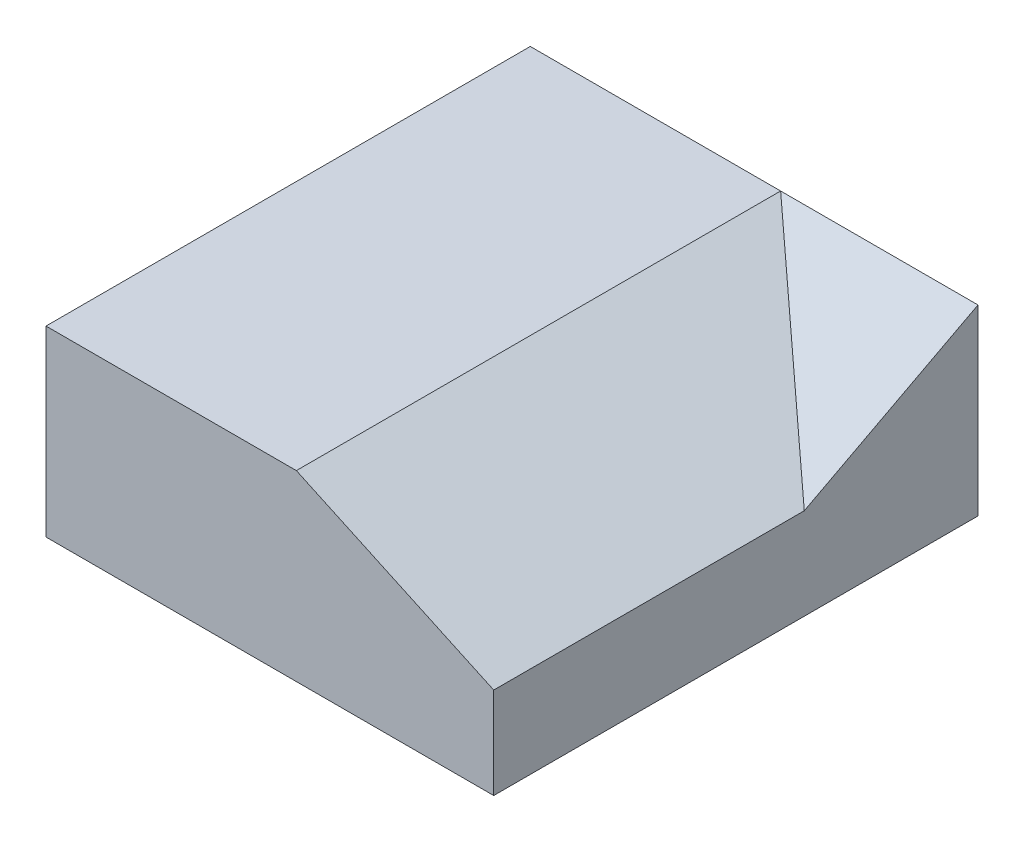
SolidWorks part; units mm, degrees
ref_plane "Front Plane" through (0, 0, 0) normal (0, 0, 1) x (1, 0, 0)
ref_plane "Top Plane" through (0, 0, 0) normal (0, 1, 0) x (1, 0, 0)
ref_plane "Right Plane" through (0, 0, 0) normal (1, 0, 0) x (0, 0, -1)
sketch "Sketch1" plane through (0, 0, 0) normal (0, 1, 0) x (1, 0, 0)
  line L1 (-30.6998, -27.7479) -> (18.3002, -27.7479)
  line L2 (-30.6998, -27.7479) -> (-30.6998, 25.2521)
  line L3 (-30.6998, 25.2521) -> (18.3002, 25.2521)
  line L4 (18.3002, -27.7479) -> (18.3002, 25.2521)
extrude "Boss-Extrude1" add sketch "Sketch1" along normal blind 20
sketch "Sketch3" plane through (0, 0, 0) normal (0, -1, 0) x (1, 0, 0)
  line L8 (-28.6998, 25.7479) -> (-28.6998, -23.2521)
  line L9 (-28.6998, -23.2521) -> (16.3002, -23.2521)
  line L10 (16.3002, -23.2521) -> (16.3002, 25.7479)
  line L11 (16.3002, 25.7479) -> (-28.6998, 25.7479)
  line L12 (-28.6998, 25.7479) -> (-28.6998, -23.2521)
  line L13 (-28.6998, -23.2521) -> (16.3002, -23.2521)
  line L14 (16.3002, -23.2521) -> (16.3002, 25.7479)
  line L15 (16.3002, 25.7479) -> (-28.6998, 25.7479)
  dimension "D1" = 2
extrude "Cut-Extrude1" cut sketch "Sketch3" against normal blind 18
sketch "Sketch4" plane through (0, 0, 27.7479) normal (0, 0, 1) x (1, 0, 0)
  line L2 (-3.2998, 20) -> (18.3002, 20)
  line L3 (18.3002, 20) -> (18.3002, 10)
  line L5 (-3.2998, 20) -> (18.3002, 10)
  line L6 (-30.6998, 20) -> (18.3002, 20) construction
  line L7 (18.3002, 20) -> (18.3002, 0) construction
  line M5 (18.3002, 0) -> (18.3002, 20)
  line M6 (18.3002, 20) -> (-30.6998, 20)
extrude "Cut-Extrude2" cut sketch "Sketch4" against normal blind 34 contours L5 M6 M5
sketch "Sketch6" plane through (18.3002, 0, 0) normal (1, 0, 0) x (0, 0, -1)
  line L0 (25.2521, 20) -> (6.2394, 10)
  line L1 (25.2521, 20) -> (6.2521, 20)
  line L2 (6.2521, 10) -> (-27.7479, 10) construction
  line L3 (25.2521, 20) -> (6.2394, 20)
  line L4 (6.2394, 20) -> (6.2394, 10)
  line M1 (6.2521, 20) -> (6.2521, 10)
  line M6 (25.2521, 20) -> (6.2521, 20)
extrude "Cut-Extrude3" cut sketch "Sketch6" against normal blind 21.6 contours L0 M6 M1
sketch "Sketch8" plane through (0, 0, 27.7479) normal (0, 0, 1) x (1, 0, 0)
  line L2 (-1.3397, 17.9906) -> (-3.2998, 19)
  line L3 (-3.7199, 19.0925) -> (17.8801, 9.0925)
  line L4 (-1.3397, 17.9906) -> (16.3002, 9.824)
  line L5 (-3.2998, 20) -> (18.3002, 10) construction
  line L6 (-1.3397, 19.0925) -> (16.3002, 10.9259)
  line L7 (-3.2998, 20) -> (-3.2998, 18) construction
  line L8 (16.3002, 9.824) -> (18.3002, 8.794)
  line L9 (18.3002, 10) -> (18.3002, 0) construction
  line L10 (18.3002, 10) -> (18.3002, 8.794)
  line L11 (-3.2998, 20) -> (-3.2998, 19)
  line L12 (18.3002, 20) -> (-3.2998, 20) construction
  line L13 (-1.3397, 19.0925) -> (-3.2998, 20)
  line L14 (16.3002, 10.9259) -> (18.3002, 10)
  dimension "D1" = 1
extrude "Boss-Extrude4" add sketch "Sketch8" against normal blind 53
sketch "Sketch11" plane through (18.3002, 0, 0) normal (1, 0, 0) x (0, 0, -1)
  line L0 (25.2521, 20) -> (6.2521, 10.0067)
  line L1 (25.2521, 18.8701) -> (8.4003, 10.0067)
  line L2 (6.2521, 10.0067) -> (8.4003, 10.0067)
  line L3 (25.2521, 20) -> (25.2521, 18.8701)
  line L6 (25.7176, 19.115) -> (6.7176, 9.1216) construction
  dimension "D1" = 1
extrude "Boss-Extrude5" add sketch "Sketch11" against normal blind 21.6
sketch "Sketch12" plane through (0, 0, -23.2521) normal (0, 0, 1) x (1, 0, 0)
  line L0 (-3.2998, 17.8182) -> (-3.2998, 10.0067)
  line L1 (-3.2998, 10.0067) -> (15.9055, 10.0067) construction
  line L2 (-3.2998, 10.0067) -> (15.9055, 10.0067)
  line L3 (15.9055, 10.0067) -> (-0.9673, 17.8182)
  line L4 (-0.9673, 17.8182) -> (-3.2998, 17.8182)
extrude "Cut-Extrude4" cut sketch "Sketch12" along normal blind 18
sketch "Sketch13" plane through (16.3002, 0, 0) normal (-1, 0, 0) x (0, 0, 1)
  line L0 (-23.2521, 17.8182) -> (-23.2521, 9.824)
  line L1 (-23.2521, 9.824) -> (-19.9059, 9.824)
  line L2 (-23.2521, 9.824) -> (25.7479, 9.824) construction
  line L3 (-23.2521, 17.8182) -> (-19.9059, 16.0582)
  line L4 (-10.148, 10.9259) -> (-23.2521, 17.8182) construction
  line L5 (-19.9059, 16.0582) -> (-8.0529, 9.824)
  line L6 (-8.0529, 9.824) -> (-19.9059, 9.824)
extrude "Cut-Extrude5" cut sketch "Sketch13" along normal blind 18
sketch "Sketch15" plane through (0, 0, -23.2521) normal (0, 0, 1) x (1, 0, 0)
  line L0 (-3.2998, 19) -> (-3.2998, 18)
  line L1 (-3.2998, 18) -> (-1.3397, 17.9906)
  line L3 (-1.3397, 17.9906) -> (-3.2998, 19)
extrude "Boss-Extrude6" add sketch "Sketch15" along normal blind 18
sketch "Sketch16" plane through (0, 18, 0) normal (0, -1, 0) x (1, 0, 0)
  circle A0 centre (-26.2498, 23.2979) radius 1
  circle A1 centre (-5.7498, 23.2979) radius 1
  circle A2 centre (-26.2498, -20.8021) radius 1
  circle A3 centre (-5.7498, -20.8021) radius 1
extrude "Boss-Extrude7" add sketch "Sketch16" along normal blind 18
sketch "Sketch17" plane through (0, 0, -25.2521) normal (0, 0, -1) x (-1, 0, 0)
  line L0 (14.4566, 16.607) -> (12.6303, 16.0591)
  line L1 (-12.5909, 14.2567) -> (1.3684, 14.2567)
  line L2 (-12.5909, 14.2567) -> (-12.5909, 8.2742)
  line L3 (-12.5909, 8.2742) -> (1.3684, 8.2742)
  line L4 (1.3684, 14.2567) -> (1.3684, 8.2742)
  line L5 (-12.5909, 14.2567) -> (1.3684, 8.2742) construction
  line L6 (-12.5909, 8.2742) -> (1.3684, 14.2567) construction
  line L8 (14.4566, 16.607) -> (18.4563, 16.607)
  line L9 (12.6303, 16.0591) -> (12.6303, 14.207)
  line L10 (12.6303, 14.207) -> (20.6303, 14.207)
  line L11 (20.6303, 16.0591) -> (20.6303, 14.207)
  line L12 (13.5435, 16.3331) -> (20.6303, 14.207) construction
  line L13 (12.6303, 14.207) -> (19.6378, 16.3092) construction
  line L15 (18.4563, 16.607) -> (20.6303, 16.0591)
  point P0 (-5.6113, 11.2655)
  point P5 (16.6303, 15.407)
extrude "Cut-Extrude7" cut sketch "Sketch17" against normal blind 2
